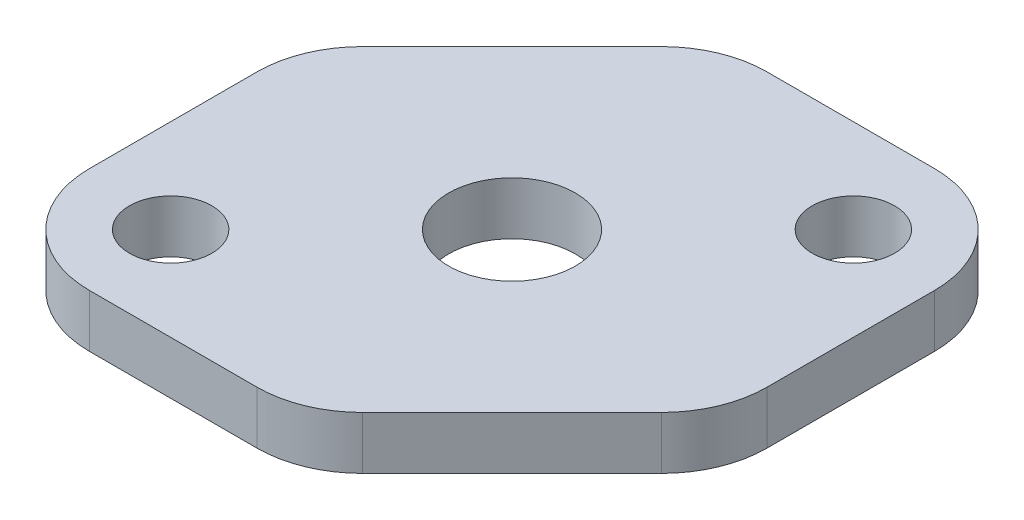
SolidWorks part; units mm, degrees
ref_plane "Front Plane" through (0, 0, 0) normal (0, 0, 1) x (1, 0, 0)
ref_plane "Top Plane" through (0, 0, 0) normal (0, 1, 0) x (1, 0, 0)
ref_plane "Right Plane" through (0, 0, 0) normal (1, 0, 0) x (0, 0, -1)
sketch "Sketch1" plane through (0, 0, 0) normal (0, 1, 0) x (1, 0, 0)
  line L1 (-15.875, -15.875) -> (15.875, -15.875)
  line L2 (-15.875, -15.875) -> (-15.875, 15.875)
  line L3 (-15.875, 15.875) -> (15.875, 15.875)
  line L4 (15.875, -15.875) -> (15.875, 15.875)
  line L5 (-15.875, -15.875) -> (15.875, 15.875) construction
  line L6 (-15.875, 15.875) -> (15.875, -15.875) construction
  point P0 (0, 0)
  dimension "D1" = 31.75
  dimension "D2" = 31.75
extrude "Boss-Extrude1" add sketch "Sketch1" along normal blind 3.175
sketch "Sketch2" plane through (0, 0, 0) normal (0, -1, 0) x (1, 0, 0)
  circle A0 centre (0, 0) radius 3.81
  dimension "D1" = 7.62
sketch "Sketch3" plane through (0, 0, 0) normal (0, -1, 0) x (1, 0, 0)
  line L0 (-15.875, 15.875) -> (15.875, -15.875) construction
  circle A0 centre (-10.2623, 10.2623) radius 2.4765
  circle A1 centre (10.2623, -10.2623) radius 2.4765
  dimension "D1" = 4.953
  dimension "D2" = 4.953
  dimension "D4" = 7.9375
  dimension "D3" = 7.9375
extrude "Cut-Extrude2" cut sketch "Sketch3" against normal through all
extrude "Cut-Extrude4" cut sketch "Sketch2" against normal through all contours A0
sketch "Sketch4" plane through (0, 3.175, 0) normal (0, 1, 0) x (1, 0, 0)
  line L0 (-15.875, 15.875) -> (-3.175, 15.875)
  line L1 (15.875, 15.875) -> (-15.875, 15.875) construction
  line L2 (-3.175, 15.875) -> (-15.875, 3.175)
  line L3 (-15.875, 15.875) -> (-15.875, -15.875) construction
  line L4 (-15.875, 3.175) -> (-15.875, 15.875)
  line L5 (15.875, -15.875) -> (15.875, -3.175)
  line L6 (15.875, -15.875) -> (15.875, 15.875) construction
  line L7 (15.875, -3.175) -> (3.175, -15.875)
  line L8 (-15.875, -15.875) -> (15.875, -15.875) construction
  line L9 (3.175, -15.875) -> (15.875, -15.875)
  dimension "D1" = 12.7
  dimension "D2" = 12.7
  dimension "D3" = 12.7
  dimension "D4" = 12.7
extrude "Cut-Extrude5" cut sketch "Sketch4" against normal through all
fillet "Fillet1" radius 6.35 6 edges at (-3.175, 1.5875, -15.875) (15.875, 1.5875, -15.875) (15.875, 1.5875, 3.175) (3.175, 1.5875, 15.875) (-15.875, 1.5875, 15.875) (-15.875, 1.5875, -3.175)
